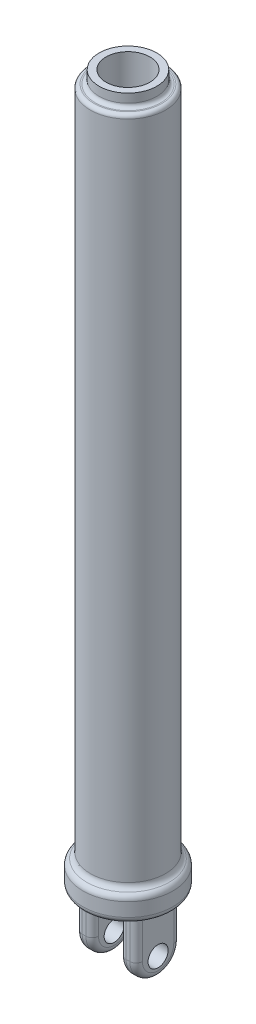
SolidWorks part; units mm, degrees
ref_plane "Front" through (0, 0, 0) normal (0, 0, 1) x (1, 0, 0)
ref_plane "Top" through (0, 0, 0) normal (0, 1, 0) x (1, 0, 0)
ref_plane "Right" through (0, 0, 0) normal (1, 0, 0) x (0, 0, -1)
sketch "Sketch1" plane through (0, 0, 0) normal (0, 0, 1) x (1, 0, 0)
  line L0 (0, 0) -> (0, 585) construction
  line L1 (-30, 552) -> (-30, 24.9774)
  line L2 (0, 565) -> (-23, 565) construction
  line L3 (0, 0) -> (-30.8239, 0)
  line L4 (-35.8239, 15.8911) -> (-35.8239, 5)
  line L5 (-27, 555) -> (-26, 555)
  line L6 (-23, 558) -> (-23, 565)
  line L7 (-17.5, 565) -> (-17.5, 40)
  line L8 (-17.5, 40) -> (0, 40)
  line L9 (-17.5, 565) -> (-23, 565)
  line L10 (0, 40) -> (0, 0)
  arc A1 (-30, 24.9774) -> (-32.9119, 20.4342) centre (-35, 24.9774) cw
  arc A2 (-35.8239, 15.8911) -> (-32.9119, 20.4342) centre (-30.8239, 15.8911) cw
  arc A3 (-30.8239, 0) -> (-35.8239, 5) centre (-30.8239, 5) cw
  arc A4 (-30, 552) -> (-27, 555) centre (-27, 552) cw
  arc A5 (-26, 555) -> (-23, 558) centre (-26, 558) ccw
  dimension "D2" = 5
  dimension "D3" = 5
  dimension "D5" = 3
  dimension "D8" = 565
  dimension "D1" = 585
  dimension "D4" = 30
  dimension "D6" = 10
  dimension "D7" = 1
  dimension "D9" = 525
  dimension "D10" = 35
revolve "Revolve1" add sketch "Sketch1" angle 360 about L10
sketch "Sketch2" plane through (0, 0, 0) normal (0, -1, 0) x (1, 0, 0)
  line L0 (0, 0) -> (0, 30.8239) construction
  line L1 (0, 0) -> (30.8239, 0) construction
  line L2 (-11, -17.5) -> (-24, 17.5) construction
  line L3 (11, 17.5) -> (24, 17.5)
  line L4 (11, 17.5) -> (11, -17.5)
  line L5 (11, -17.5) -> (24, -17.5)
  line L6 (24, 17.5) -> (24, -17.5)
  line L7 (11, 17.5) -> (24, -17.5) construction
  line L8 (11, -17.5) -> (24, 17.5) construction
  line L9 (-11, 17.5) -> (-24, -17.5) construction
  line L10 (-24, 17.5) -> (-24, -17.5)
  line L11 (-11, -17.5) -> (-24, -17.5)
  line L12 (-11, 17.5) -> (-11, -17.5)
  line L13 (-11, 17.5) -> (-24, 17.5)
  circle A0 centre (0, 0) radius 30.8239 construction
  point P6 (17.5, 0)
  point P16 (-17.5, 0)
  dimension "D1" = 35
  dimension "D2" = 48
  dimension "D3" = 22
extrude "Boss-Extrude1" add sketch "Sketch2" along normal blind 50
sketch "Sketch3" plane through (24, 0, 0) normal (1, 0, 0) x (0, 0, -1)
  line L0 (-17.5, -32.5) -> (-17.5, -50)
  line L1 (-17.5, -50) -> (17.5, -50)
  line L2 (17.5, -50) -> (17.5, -32.5)
  line L3 (-30.8239, 0) -> (30.8239, 0) construction
  arc A0 (-17.5, -32.5) -> (17.5, -32.5) centre (0, -32.5) ccw
  circle A2 centre (0, -35) radius 8
  dimension "D1" = 16
  dimension "D2" = 35
extrude "Cut-Extrude1" cut sketch "Sketch3" against normal through all
fillet "Fillet1" radius 5 12 edges at (24, -16.25, 17.5) (24, -16.25, -17.5) (11, -16.25, 17.5) (11, -16.25, -17.5) (-11, -16.25, -17.5) (-11, -16.25, 17.5) (-24, -16.25, 17.5) (-24, -16.25, -17.5) (24, -50, 0) (11, -50, 0) (-11, -50, 0) (-24, -50, 0)
